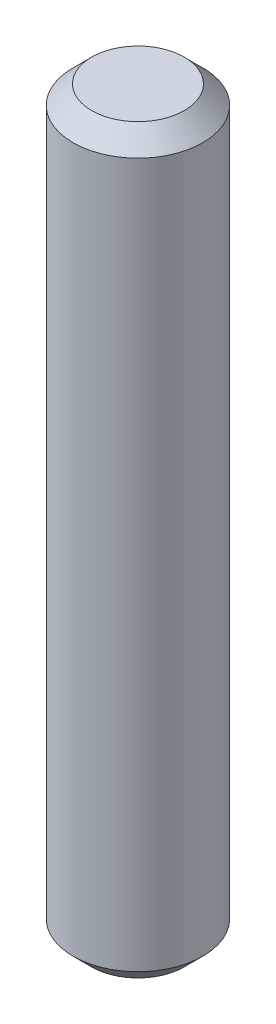
SolidWorks part; units mm, degrees
ref_plane "Front Plane" through (0, 0, 0) normal (0, 0, 1) x (1, 0, 0)
ref_plane "Top Plane" through (0, 0, 0) normal (0, 1, 0) x (1, 0, 0)
ref_plane "Right Plane" through (0, 0, 0) normal (1, 0, 0) x (0, 0, -1)
sketch "Sketch1" plane through (0, 0, 0) normal (0, 1, 0) x (1, 0, 0)
  circle A0 centre (0, 0) radius 3.5
  dimension "D1" = 7
extrude "Boss-Extrude1" add sketch "Sketch1" along normal blind 40
chamfer "Chamfer1" distance 1 angle 45 2 edges at (0, 0, 3.5) (0, 40, 3.5)
